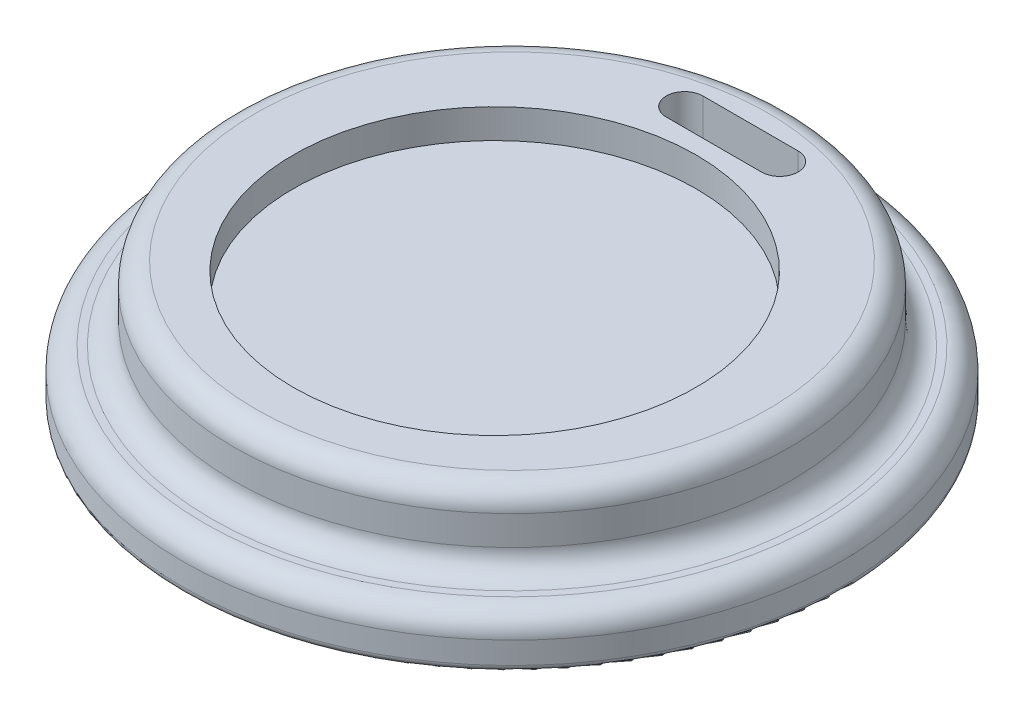
SolidWorks part; units mm, degrees
ref_plane "Front Plane" through (0, 0, 0) normal (0, 0, 1) x (1, 0, 0)
ref_plane "Top Plane" through (0, 0, 0) normal (0, 1, 0) x (1, 0, 0)
ref_plane "Right Plane" through (0, 0, 0) normal (1, 0, 0) x (0, 0, -1)
sketch "Sketch1" plane through (0, 0, 0) normal (1, 0, 0) x (0, 0, -1)
  line L0 (0, 0) -> (43, 0)
  line L1 (43, 0) -> (43, -5)
  line L2 (43, -5) -> (44, -5)
  line L10 (45, -4) -> (45, -1)
  line L11 (42, 2) -> (41, 2)
  line L12 (38, 5) -> (38, 9)
  line L13 (35, 12) -> (0, 12)
  line L14 (0, 12) -> (0, 0)
  arc A0 (38, 9) -> (35, 12) centre (35, 9) ccw
  arc A1 (38, 5) -> (41, 2) centre (41, 5) ccw
  arc A2 (45, -1) -> (42, 2) centre (42, -1) ccw
  arc A3 (44, -5) -> (45, -4) centre (44, -4) ccw
  point P11 (38, 12)
  point P14 (38, 2)
  point P19 (45, -5)
  dimension "D7" = 3
  dimension "D8" = 1
  dimension "D1" = 2
  dimension "D2" = 2
  dimension "D3" = 5
  dimension "D4" = 43
  dimension "D5" = 10
  dimension "D6" = 7
revolve "Revolve1" add sketch "Sketch1" angle 360 about L14
sketch "Sketch2" plane through (0, 12, 0) normal (0, 1, 0) x (1, 0, 0)
  line L0 (0, -35) -> (0, -30) construction
  circle A0 centre (0, -2.3683) radius 27.5
  circle A1 centre (0, 0) radius 35 construction
  dimension "D2" = 55
  dimension "D1" = 5
extrude "Cut-Extrude1" cut sketch "Sketch2" against normal blind 4
sketch "Sketch3" plane through (0, 12, 0) normal (0, 1, 0) x (1, 0, 0)
  line L0 (0, 25.1317) -> (0, 35) construction
  line L1 (-6.5, 30.0659) -> (6.5, 30.0659) construction
  line L2 (-6.5, 32.5659) -> (6.5, 32.5659)
  line L3 (-6.5, 27.5659) -> (6.5, 27.5659)
  circle A0 centre (0, -2.3683) radius 27.5 construction
  circle A1 centre (0, -2.3683) radius 27.5 construction
  circle A2 centre (0, 0) radius 35 construction
  arc A3 (-6.5, 32.5659) -> (-6.5, 27.5659) centre (-6.5, 30.0659) ccw
  arc A4 (6.5, 27.5659) -> (6.5, 32.5659) centre (6.5, 30.0659) ccw
  point P11 (0, 30.0659)
  dimension "D1" = 13
  dimension "D2" = 5
extrude "Cut-Extrude2" cut sketch "Sketch3" against normal blind 28
